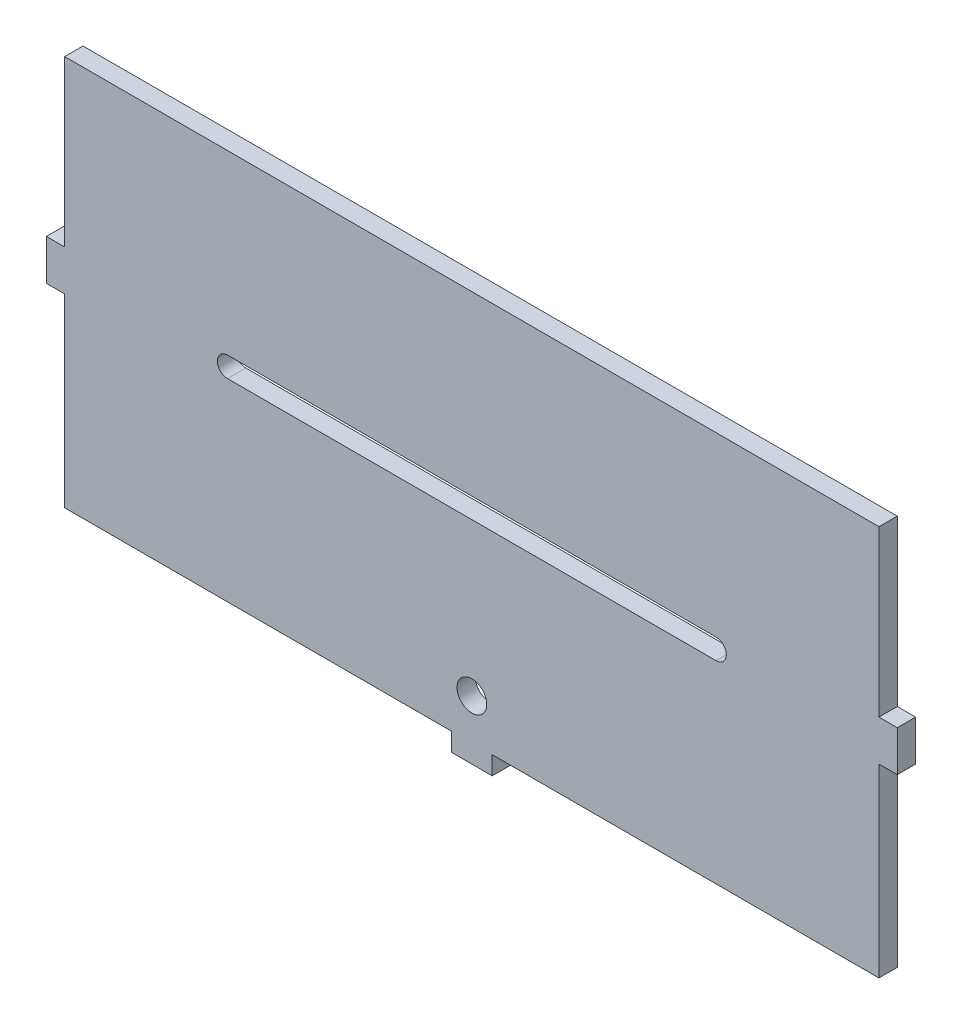
SolidWorks part; units mm, degrees
ref_plane "Front Plane" through (0, 0, 0) normal (0, 0, 1) x (1, 0, 0)
ref_plane "Top Plane" through (0, 0, 0) normal (0, 1, 0) x (1, 0, 0)
ref_plane "Right Plane" through (0, 0, 0) normal (1, 0, 0) x (0, 0, -1)
sketch "Sketch1" plane through (0, 0, 0) normal (0, 0, 1) x (1, 0, 0)
  line L0 (6.35, -63.5) -> (127, -63.5)
  line L1 (-127, -63.5) -> (-6.35, -63.5)
  line L2 (-127, -63.5) -> (-127, -5.715)
  line L3 (-127, 63.5) -> (127, 63.5)
  line L4 (127, -63.5) -> (127, -5.715)
  line L5 (-127, -63.5) -> (127, 63.5) construction
  line L6 (-127, 63.5) -> (127, -63.5) construction
  line L7 (-6.35, -69.215) -> (6.35, -69.215)
  line L8 (-6.35, -69.215) -> (-6.35, -63.5)
  line L10 (6.35, -69.215) -> (6.35, -63.5)
  line L11 (-127, 6.985) -> (-127, 63.5)
  line L12 (-132.715, -5.715) -> (-127, -5.715)
  line L13 (-132.715, -5.715) -> (-132.715, 6.985)
  line L14 (-132.715, 6.985) -> (-127, 6.985)
  line L16 (0, -55) -> (0, 55) construction
  line L17 (132.715, -5.715) -> (127, -5.715)
  line L18 (132.715, -5.715) -> (132.715, 6.985)
  line L19 (132.715, 6.985) -> (127, 6.985)
  line L20 (127, 6.985) -> (127, 63.5)
  point P0 (0, 0)
  point P6 (0, -63.5)
  point P10 (-127, 0)
  dimension "D1" = 127
  dimension "D2" = 254
  dimension "D3" = 12.7
  dimension "D4" = 5.715
  dimension "D5" = 12.7
  dimension "D6" = 57.785
extrude "Boss-Extrude1" add sketch "Sketch1" along normal blind 5.715
sketch "Sketch2" plane through (0, 0, 5.715) normal (0, 0, 1) x (1, 0, 0)
  line L0 (76.2, 0) -> (-76.2, 0) construction
  line L1 (76.2, -3.175) -> (-76.2, -3.175)
  line L2 (76.2, 3.175) -> (-76.2, 3.175)
  arc A0 (76.2, -3.175) -> (76.2, 3.175) centre (76.2, 0) ccw
  arc A1 (-76.2, 3.175) -> (-76.2, -3.175) centre (-76.2, 0) ccw
  point P3 (0, 0)
  dimension "D1" = 152.4
  dimension "D2" = 6.35
extrude "Cut-Extrude1" cut sketch "Sketch2" against normal through all
sketch "Sketch4" plane through (0, 0, 5.715) normal (0, 0, 1) x (1, 0, 0)
  line L0 (6.35, -63.5) -> (127, -63.5) construction
  circle A0 centre (0, -50.8) radius 4.6355
  dimension "D1" = 9.271
  dimension "D2" = 12.7
extrude "Cut-Extrude2" cut sketch "Sketch4" against normal through all both
sketch "Sketch5" plane through (0, 0, 5.715) normal (0, 0, 1) x (1, 0, 0)
  line L0 (-127, 58.42) -> (127, 58.42)
  line L1 (-127, 63.5) -> (-127, 6.985) construction
  line L2 (127, 6.985) -> (127, 63.5) construction
  line L3 (127, 63.5) -> (-127, 63.5) construction
  line L4 (-127, 58.42) -> (-127, 63.5)
  line L5 (-127, 63.5) -> (127, 63.5)
  line L6 (127, 63.5) -> (127, 58.42)
  dimension "D1" = 5.08
extrude "Cut-Extrude3" cut sketch "Sketch5" against normal through all
